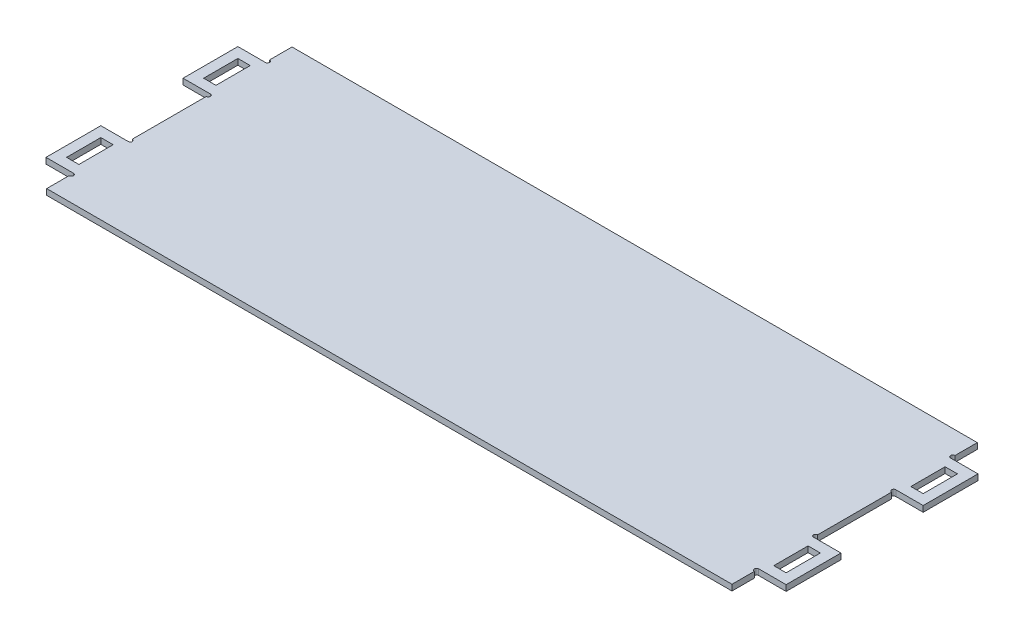
SolidWorks part; units mm, degrees
material "Teak"
ref_plane "Front Plane" through (0, 0, 0) normal (0, 0, 1) x (1, 0, 0)
ref_plane "Top Plane" through (0, 0, 0) normal (0, 1, 0) x (1, 0, 0)
ref_plane "Right Plane" through (0, 0, 0) normal (1, 0, 0) x (0, 0, -1)
sketch "Sketch1" plane through (0, 0, 0) normal (0, 1, 0) x (1, 0, 0)
  line L0 (-1000, 0) -> (49000, 0) construction
  line L1 (-500, 179) -> (500, 179)
  line L2 (-500, 179) -> (-500, 146.36)
  line L3 (-500, -179) -> (500, -179)
  line L4 (500, 179) -> (500, 146.36)
  line L5 (-500, 179) -> (500, -179) construction
  line L6 (-500, -179) -> (500, 179) construction
  line L7 (-507, 75) -> (-507, 125)
  line L8 (-500, -60) -> (-540, -60)
  line L9 (-500, -60) -> (-500, -140)
  line L10 (-500, -140) -> (-540, -140)
  line L11 (-540, -60) -> (-540, -140)
  line L12 (-525, -75) -> (-507, -75)
  line L13 (-525, -75) -> (-525, -125)
  line L14 (-525, -125) -> (-507, -125)
  line L15 (-507, -75) -> (-507, -125)
  line L16 (-525, 125) -> (-507, 125)
  line L17 (-525, 75) -> (-525, 125)
  line L18 (-525, 75) -> (-507, 75)
  line L19 (-540, 60) -> (-540, 140)
  line L20 (-500, 140) -> (-540, 140)
  line L21 (-500, 60) -> (-540, 60)
  line L22 (0, -1000) -> (0, 49000) construction
  line L23 (507, -75) -> (507, -125)
  line L24 (525, -125) -> (507, -125)
  line L25 (525, -75) -> (525, -125)
  line L26 (525, -75) -> (507, -75)
  line L27 (540, -60) -> (540, -140)
  line L28 (500, -140) -> (540, -140)
  line L29 (500, -60) -> (540, -60)
  line L30 (500, 60) -> (540, 60)
  line L31 (500, 140) -> (540, 140)
  line L32 (540, 60) -> (540, 140)
  line L33 (525, 75) -> (507, 75)
  line L34 (525, 75) -> (525, 125)
  line L35 (525, 125) -> (507, 125)
  line L36 (507, 75) -> (507, 125)
  line L37 (-500, -146.36) -> (-500, -179)
  line L38 (-500, -60) -> (-500, -140)
  line L39 (-500, 140) -> (-500, 60)
  line L40 (-500, 54) -> (-500, -54)
  line L41 (500, 140) -> (500, 60)
  line L42 (500, 54) -> (500, -54)
  line L43 (500, -60) -> (500, -140)
  line L44 (500, -146.36) -> (500, -179)
  arc A0 (-500, -140) -> (-500, -146.36) centre (-500, -143.18) cw
  arc A1 (-500, -60) -> (-500, -54) centre (-500, -57) ccw
  arc A2 (-500, 60) -> (-500, 54) centre (-500, 57) cw
  arc A3 (-500, 140) -> (-500, 146.36) centre (-500, 143.18) ccw
  arc A4 (500, -60) -> (500, -54) centre (500, -57) cw
  arc A5 (500, -140) -> (500, -146.36) centre (500, -143.18) ccw
  arc A6 (500, 140) -> (500, 146.36) centre (500, 143.18) cw
  arc A7 (500, 60) -> (500, 54) centre (500, 57) ccw
  point P0 (0, 0)
  point P42 (-525, -100)
  point P43 (-540, -100)
  dimension "D9" = 3
  dimension "D10" = 3.18
  dimension "D1" = 1000
  dimension "D2" = 358
  dimension "D3" = 80
  dimension "D4" = 50
  dimension "D5" = 40
  dimension "D6" = 15
  dimension "D7" = 18
  dimension "D8" = 60
extrude "Boss-Extrude1" add sketch "Sketch1" along normal mid plane 8.6 contours L4 L1 L2 L3 | L21 L2 L20 L19 L18 L17 L16 L7 | L8 L11 L10 L2 L12 L15 L14 L13 | L30 L32 L31 L4 L33 L36 L35 L34 | L29 L4 L28 L27 L26 L25 L24 L23
